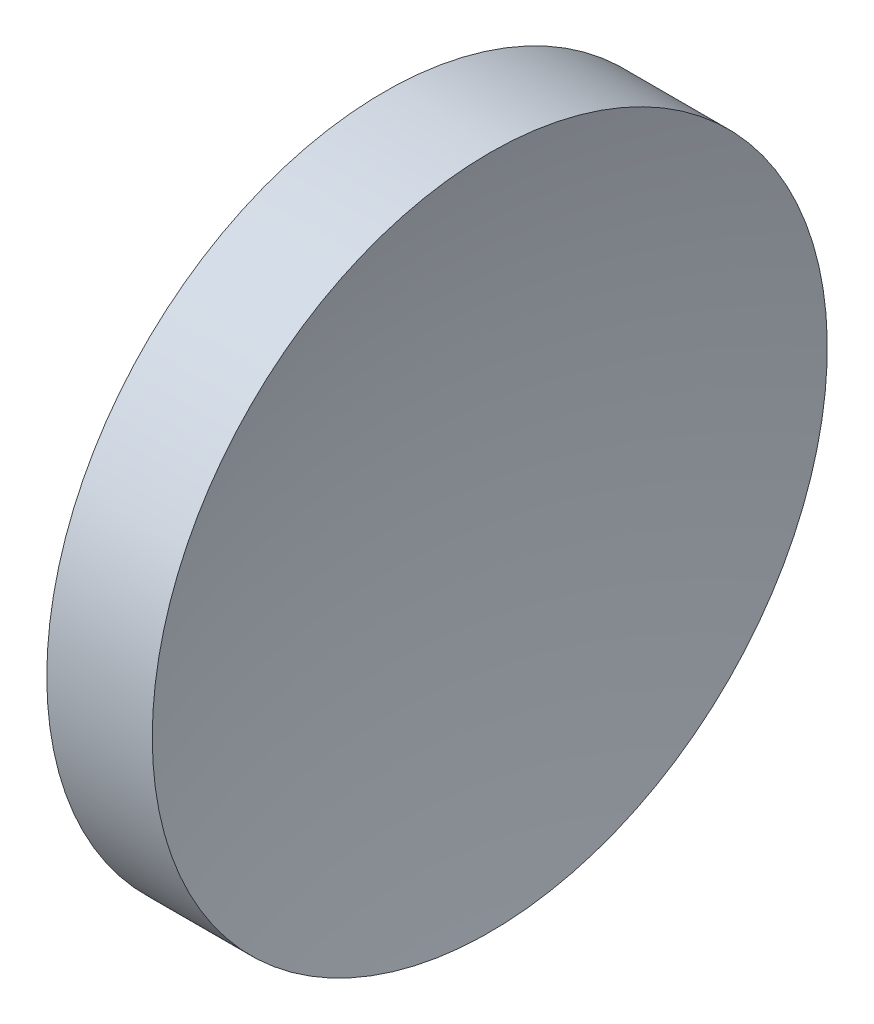
SolidWorks part; units mm, degrees
ref_plane "前视基准面" through (0, 0, 0) normal (0, 0, 1) x (1, 0, 0)
ref_plane "上视基准面" through (0, 0, 0) normal (0, 1, 0) x (1, 0, 0)
ref_plane "右视基准面" through (0, 0, 0) normal (1, 0, 0) x (0, 0, -1)
sketch "草图1" plane through (0, 0, 0) normal (0, 0, 1) x (1, 0, 0)
  line L0 (42.4499, 26.089) -> (50.324, 26.089) construction
  line L1 (44.3192, 26.089) -> (44.3192, 34.089)
  line L2 (45.8192, 26.089) -> (44.3192, 26.089)
  line L3 (44.3192, 34.089) -> (46.8192, 34.089)
  arc A0 (46.8192, 34.089) -> (45.8192, 26.089) centre (78.3192, 26.089) ccw
  dimension "D3" = 32.5
  dimension "D1" = 8
  dimension "D2" = 2.5
revolve "旋转1" add sketch "草图1" angle 360 about L0
